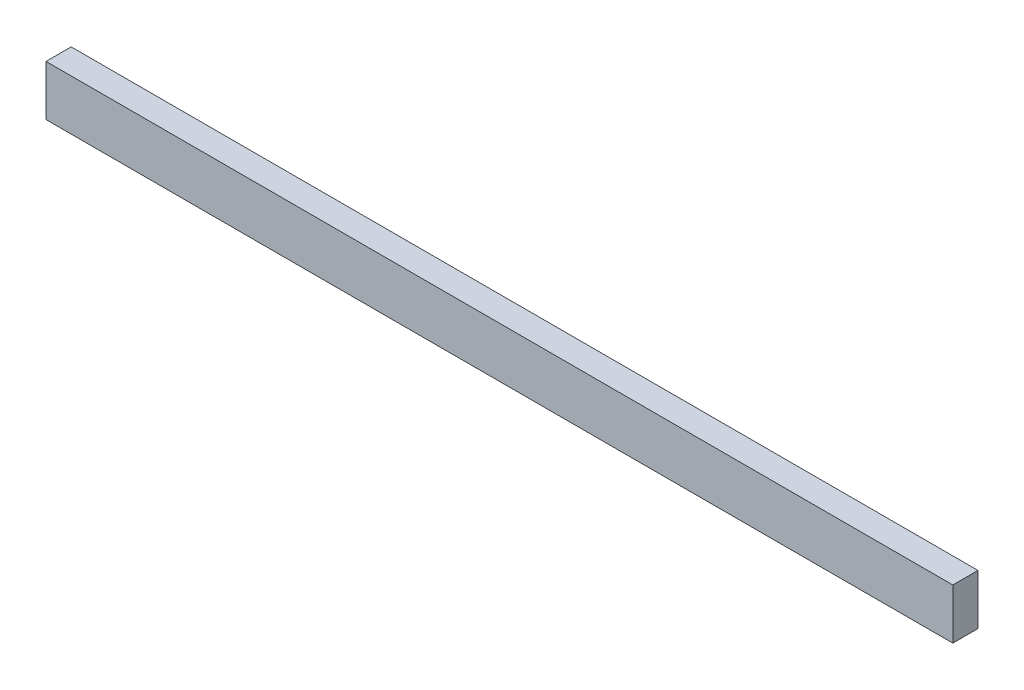
SolidWorks part; units mm, degrees
ref_plane "Front Plane" through (0, 0, 0) normal (0, 0, 1) x (1, 0, 0)
ref_plane "Top Plane" through (0, 0, 0) normal (0, 1, 0) x (1, 0, 0)
ref_plane "Right Plane" through (0, 0, 0) normal (1, 0, 0) x (0, 0, -1)
sketch "Sketch1" plane through (0, 0, 0) normal (0, 0, 1) x (1, 0, 0)
  line L1 (-209.6982, 50.4779) -> (150.3018, 50.4779)
  line L2 (-209.6982, 50.4779) -> (-209.6982, 30.4779)
  line L3 (-209.6982, 30.4779) -> (150.3018, 30.4779)
  line L4 (150.3018, 50.4779) -> (150.3018, 30.4779)
  line L5 (-209.6982, 50.4779) -> (150.3018, 30.4779) construction
  line L6 (-209.6982, 30.4779) -> (150.3018, 50.4779) construction
  point P0 (-29.6982, 40.4779)
  dimension "D1" = 360
  dimension "D2" = 20
extrude "Boss-Extrude1" add sketch "Sketch1" along normal blind 10
